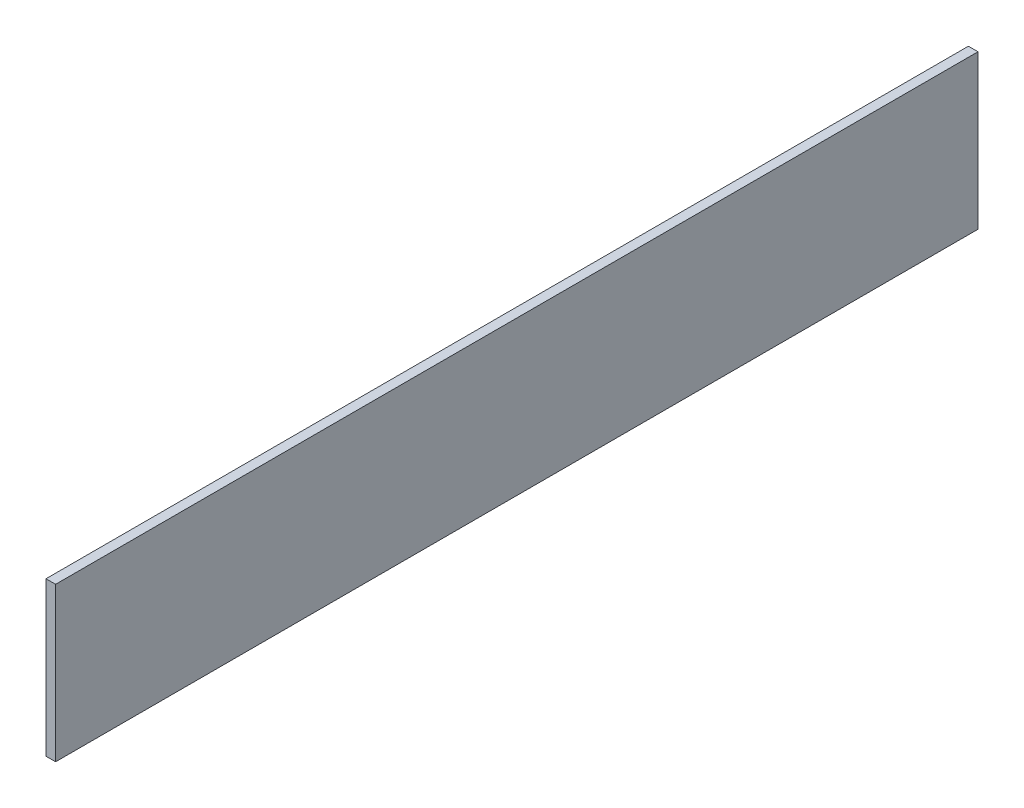
SolidWorks part; units mm, degrees
ref_plane "Front Plane" through (0, 0, 0) normal (0, 0, 1) x (1, 0, 0)
ref_plane "Top Plane" through (0, 0, 0) normal (0, 1, 0) x (1, 0, 0)
ref_plane "Right Plane" through (0, 0, 0) normal (1, 0, 0) x (0, 0, -1)
sketch "Sketch1" plane through (0, 0, 0) normal (1, 0, 0) x (0, 0, -1)
  line L1 (0, 0) -> (152.4, 0)
  line L2 (0, 0) -> (0, 25.4)
  line L3 (0, 25.4) -> (152.4, 25.4)
  line L4 (152.4, 0) -> (152.4, 25.4)
  dimension "D1" = 152.4
  dimension "D2" = 25.4
extrude "Boss-Extrude1" add sketch "Sketch1" along normal blind 1.5875
